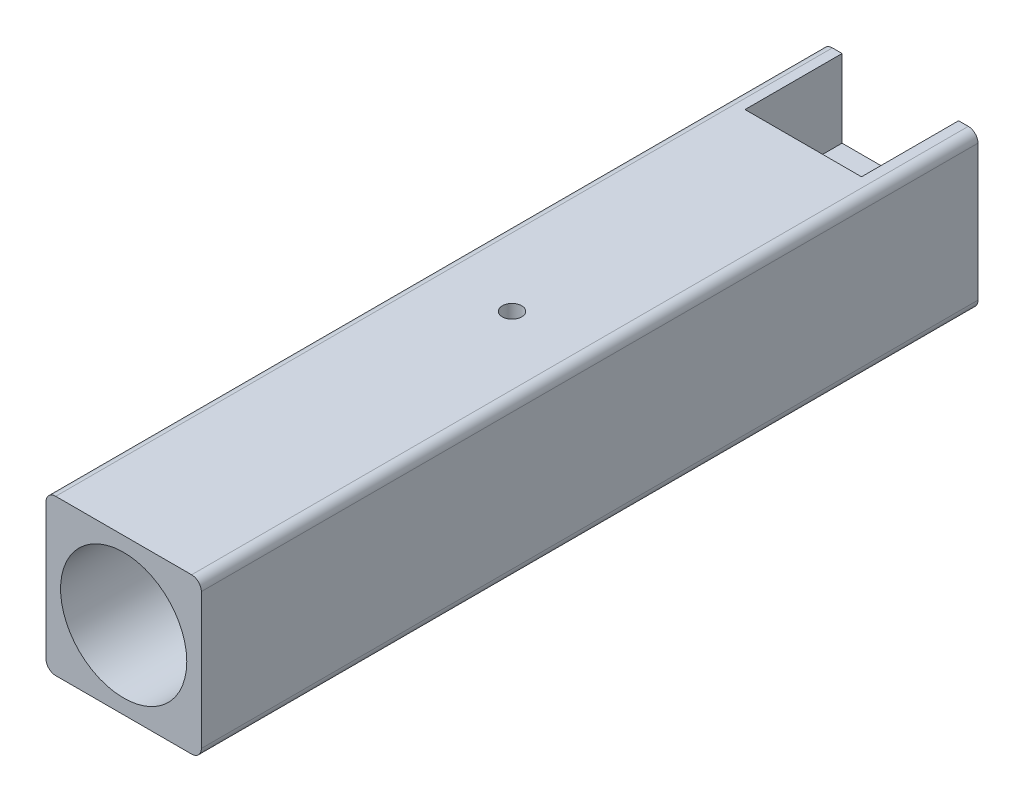
SolidWorks part; units mm, degrees
ref_plane "前视基准面" through (0, 0, 0) normal (0, 0, 1) x (1, 0, 0)
ref_plane "上视基准面" through (0, 0, 0) normal (0, 1, 0) x (1, 0, 0)
ref_plane "右视基准面" through (0, 0, 0) normal (1, 0, 0) x (0, 0, -1)
other "Configuration Table"
sketch "草图1" plane through (0, 0, 0) normal (0, 0, 1) x (1, 0, 0)
  line L1 (0, 0) -> (16, 0)
  line L2 (0, 0) -> (0, -16)
  line L3 (0, -16) -> (16, -16)
  line L4 (16, 0) -> (16, -16)
  line L5 (0, 0) -> (16, -16) construction
  line L6 (0, -16) -> (16, 0) construction
  point P4 (8, -8)
  dimension "D1" = 16
  dimension "D2" = 16
extrude "凸台-拉伸1" add sketch "草图1" along normal blind 80
sketch "草图2" plane through (0, 0, 80) normal (0, 0, 1) x (1, 0, 0)
  line L0 (0, 0) -> (16, -16) construction
  circle A0 centre (8, -8) radius 6.5
  dimension "D1" = 13
extrude "切除-拉伸1" cut sketch "草图2" against normal blind 50
sketch "草图10" plane through (0, 0, 0) normal (0, 0, -1) x (-1, 0, 0)
  line L0 (-14, -8) -> (-14, -13) construction
  line L1 (-16, 0) -> (0, 0) construction
  line L2 (-16, 0) -> (-16, -16) construction
  line L3 (-16, -16) -> (0, -16) construction
  line L4 (0, 0) -> (0, -16) construction
  line L5 (-16, 0) -> (0, -16) construction
  line L6 (-16, -16) -> (0, 0) construction
  line L7 (-14, 0) -> (-2, 0)
  line L8 (-14, 0) -> (-14, -8)
  line L9 (-14, -8) -> (-2, -8)
  line L10 (-2, 0) -> (-2, -8)
  line L11 (-14, 0) -> (-2, -8) construction
  line L12 (-14, -8) -> (-2, 0) construction
  line L14 (-14, -13) -> (-2, -13)
  line L15 (-14, -13) -> (-14, -16)
  line L16 (-14, -16) -> (-2, -16)
  line L17 (-2, -13) -> (-2, -16)
  line L18 (-14, -13) -> (-2, -16) construction
  line L19 (-14, -16) -> (-2, -13) construction
  point P4 (-8, -8)
  point P11 (-8, -4)
  point P16 (-8, -14.5)
  dimension "D1" = 2
  dimension "D2" = 2
  dimension "D3" = 8
  dimension "D4" = 5
extrude "切除-拉伸2" cut sketch "草图10" against normal blind 10
sketch "草图11" plane through (0, -13, 0) normal (0, -1, 0) x (1, 0, 0)
  line L1 (2, 10) -> (14, 10) construction
  line L2 (2, 10) -> (2, 0) construction
  line L3 (2, 0) -> (14, 0) construction
  line L4 (14, 10) -> (14, 0) construction
  line L5 (2, 10) -> (14, 0) construction
  line L6 (2, 0) -> (14, 10) construction
  circle A0 centre (8, 5) radius 3.25
  point P4 (8, 5)
  dimension "D1" = 6.5
extrude "切除-拉伸5" cut sketch "草图11" against normal blind 1
hole_wizard "M4 螺纹孔的螺纹孔钻头1" positions "草图12" profile "草图13" hole size "M4" standard "ISO" end condition up to next
sketch "草图12" plane through (0, -12, 0) normal (0, -1, 0) x (-1, 0, 0)
  point P0 (-8, -5)
sketch "草图13" plane through (8, -12, 5) normal (1, 0, 0) x (0, 0, -1)
  line L0 (0, 0) -> (0, 4)
  line L1 (0, 4) -> (1.65, 4)
  line L2 (1.65, 4) -> (1.65, 0)
  line L5 (1.65, 0) -> (0, 0)
  line L11 (0, -6.35) -> (0, 107.95) construction
  dimension "通孔孔直径" = 3.3
  dimension "通孔孔深度" = 4
sketch "草图14" plane through (0, 0, 0) normal (0, 1, 0) x (1, 0, 0)
  line L0 (0, -80) -> (0, 0) construction
  line L1 (16, -80) -> (0, -80) construction
  line L2 (16, -80) -> (16, -40) construction
  line L3 (16, -40) -> (0, -40) construction
  line L4 (0, -80) -> (0, -40) construction
  line L5 (16, -80) -> (0, -40) construction
  line L6 (16, -40) -> (0, -80) construction
  circle A0 centre (8, -40) radius 1
  point P4 (8, -60)
  dimension "D2" = 2
  dimension "D1" = 40
extrude "切除-拉伸6" cut sketch "草图14" against normal up to next
fillet "圆角1" radius 1 4 edges at (16, -16, 40) (16, 0, 40) (0, 0, 40) (0, -16, 40)
